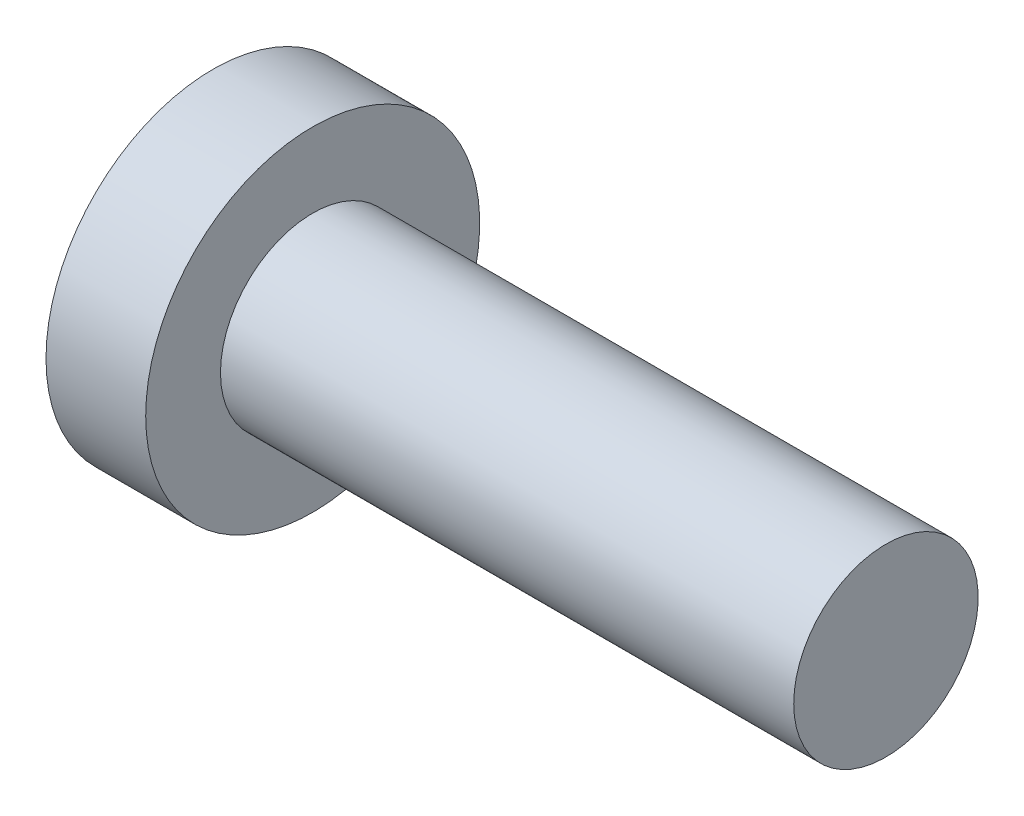
SolidWorks part; units mm, degrees
ref_plane "Front Plane" through (0, 0, 0) normal (0, 0, 1) x (1, 0, 0)
ref_plane "Top Plane" through (0, 0, 0) normal (0, 1, 0) x (1, 0, 0)
ref_plane "Right Plane" through (0, 0, 0) normal (1, 0, 0) x (0, 0, -1)
sketch "Sketch1" plane through (0, 0, 0) normal (0, 0, 1) x (1, 0, 0)
  line L0 (0, 0) -> (17661.4653, 0) construction
  line L1 (-13.5, 0) -> (-13.5, 6.7)
  line L2 (-13.5, 6.7) -> (-9.5, 6.7)
  line L3 (-9.5, 6.7) -> (-9.5, 3.7)
  line L4 (-9.5, 3.7) -> (13.5, 3.7)
  line L5 (13.5, 3.7) -> (13.5, 0)
  line L6 (0, 0) -> (0, -50000) construction
  line L7 (-13.5, 0) -> (13.5, 0)
  dimension "D1" = 3.7
  dimension "D2" = 4
  dimension "D3" = 3
  dimension "D4" = 27
revolve "Revolve1" add sketch "Sketch1" angle 360 about L0
